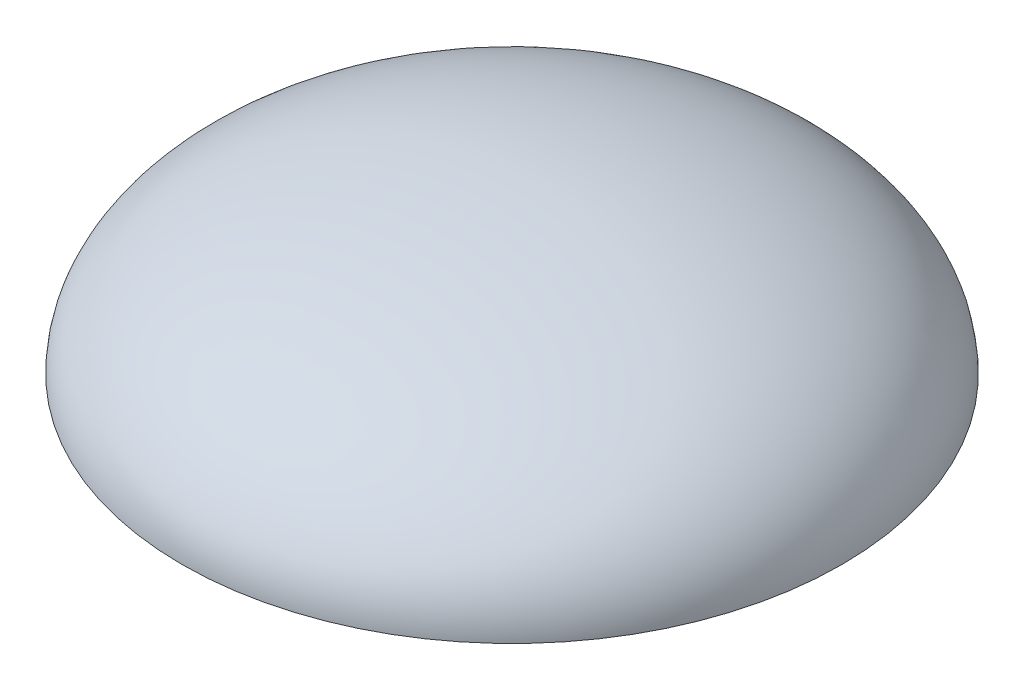
SolidWorks part; units mm, degrees
material "Acrylic (Medium-high impact)"
ref_plane "Front" through (0, 0, 0) normal (0, 0, 1) x (1, 0, 0)
ref_plane "Top" through (0, 0, 0) normal (0, 1, 0) x (1, 0, 0)
ref_plane "Right" through (0, 0, 0) normal (1, 0, 0) x (0, 0, -1)
sketch "Sketch1" plane through (0, 0, 0) normal (0, 0, 1) x (1, 0, 0)
  line L0 (-13.25, 0) -> (0, 0)
  line L1 (0, 6.5) -> (0, 0)
  ellipse E0 centre (0, 0) end of major axis (13.25, 0) minor radius 6.5 (0, 6.5) -> (-13.25, 0) ccw
  dimension "D1" = 6.5
  dimension "D2" = 13.25
revolve "Revolve1" add sketch "Sketch1" angle 360 about L1
shell "Shell1" thickness 3
